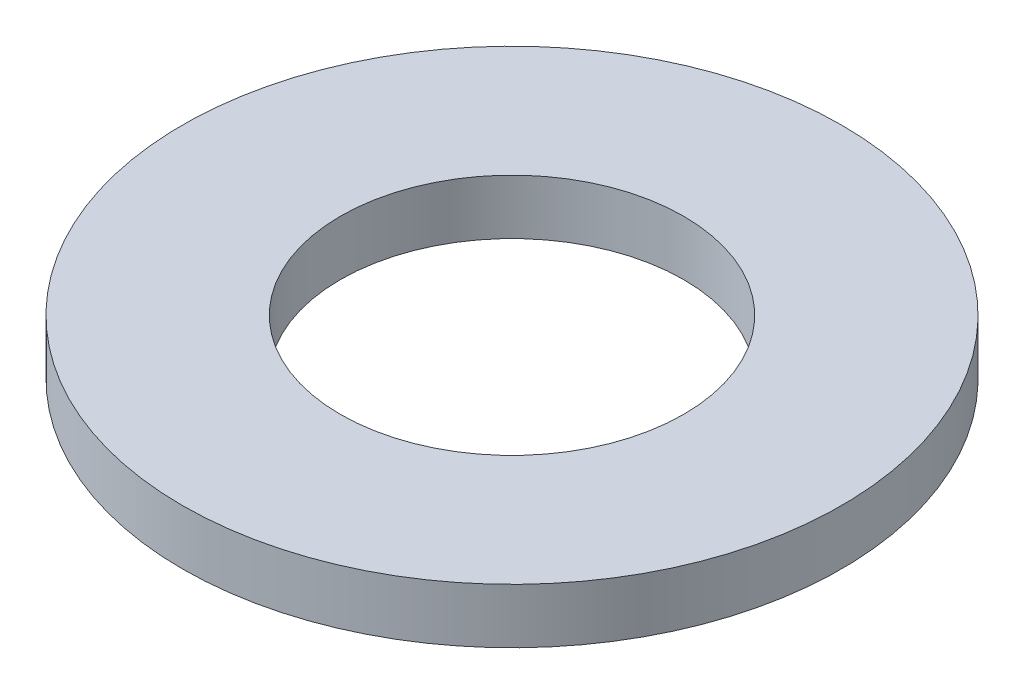
SolidWorks part; units mm, degrees
ref_plane "Front Plane" through (0, 0, 0) normal (0, 0, 1) x (1, 0, 0)
ref_plane "Top Plane" through (0, 0, 0) normal (0, 1, 0) x (1, 0, 0)
ref_plane "Right Plane" through (0, 0, 0) normal (1, 0, 0) x (0, 0, -1)
sketch "Sketch1" plane through (0, 0, 0) normal (0, 1, 0) x (1, 0, 0)
  circle A0 centre (0, 0) radius 6
  circle A1 centre (0, 0) radius 3.125
  dimension "D1" = 12
  dimension "D2" = 6.25
extrude "Boss-Extrude1" add sketch "Sketch1" along normal blind 1
